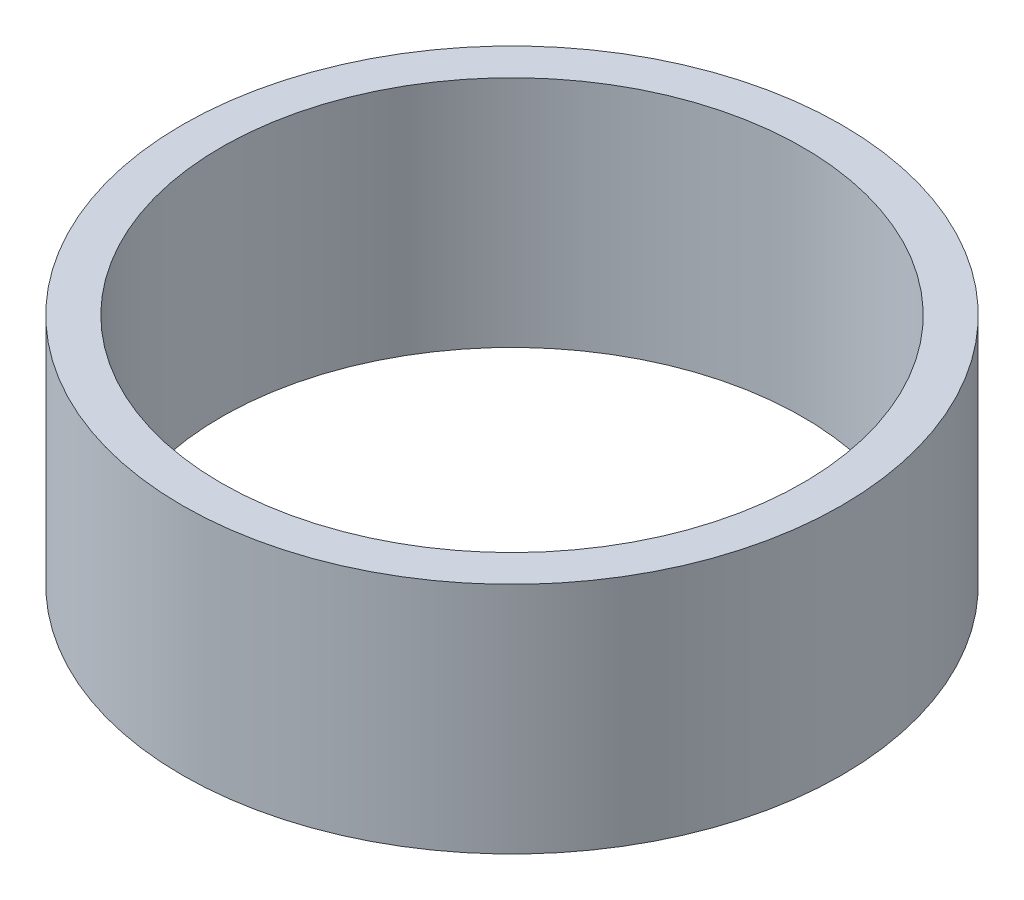
SolidWorks part; units mm, degrees
ref_plane "Front Plane" through (0, 0, 0) normal (0, 0, 1) x (1, 0, 0)
ref_plane "Top Plane" through (0, 0, 0) normal (0, 1, 0) x (1, 0, 0)
ref_plane "Right Plane" through (0, 0, 0) normal (1, 0, 0) x (0, 0, -1)
sketch "Sketch1" plane through (0, 0, 0) normal (0, 1, 0) x (1, 0, 0)
  line L0 (0, 37.35) -> (0, 42.35)
  circle A0 centre (0, 0) radius 37.35
  circle A1 centre (0, 0) radius 42.35
  dimension "D2" = 74.7
  dimension "D1" = 5
extrude "Boss-Extrude1" add sketch "Sketch1" along normal blind 30
